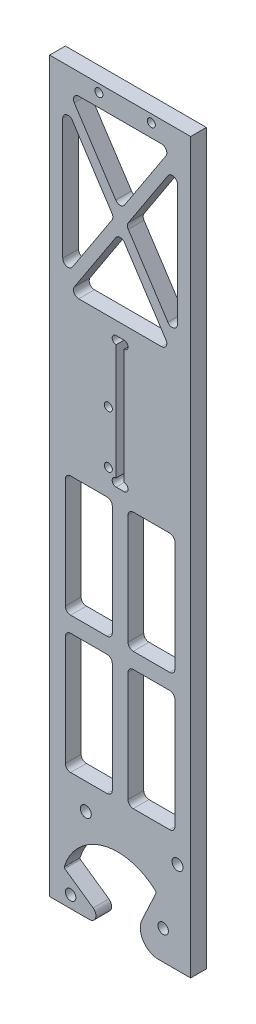
SolidWorks part; units mm, degrees
material "Thornel Mat VMA"
ref_plane "前视基准面" through (0, 0, 0) normal (0, 0, 1) x (1, 0, 0)
ref_plane "上视基准面" through (0, 0, 0) normal (0, 1, 0) x (1, 0, 0)
ref_plane "右视基准面" through (0, 0, 0) normal (1, 0, 0) x (0, 0, -1)
sketch "草图1" plane through (0, 0, 0) normal (0, 0, 1) x (1, 0, 0)
  line L1 (-33.5, 15) -> (33.5, 15)
  line L2 (-33.5, 15) -> (-33.5, -15)
  line L3 (-33.5, -15) -> (33.5, -15)
  line L4 (33.5, 15) -> (33.5, -15)
  line L5 (-33.5, 15) -> (33.5, -15) construction
  line L6 (-33.5, -15) -> (33.5, 15) construction
  point P0 (0, 0)
  dimension "D1" = 30
  dimension "D2" = 67
extrude "凸台-拉伸1" add sketch "草图1" along normal blind 6
sketch "草图3" plane through (0, 0, 6) normal (0, 0, 1) x (1, 0, 0)
  line L0 (0.156, -18.5) -> (0, 0) construction
  line L1 (33.5, -15) -> (33.5, 15) construction
  circle A0 centre (0.156, -18.5) radius 11.5
  dimension "D2" = 23
  dimension "D1" = 18.5
  dimension "D3" = 0.483
extrude "切除-拉伸1" cut sketch "草图3" against normal through all
sketch "草图4" plane through (0, 0, 6) normal (0, 0, 1) x (1, 0, 0)
  line L0 (0.156, -18.5) -> (0.156, 2.75) construction
  line L1 (14.9513, -3.2467) -> (0.156, -34.9754)
  line L2 (-20.2837, -12.6879) -> (0.156, -27)
  line L3 (0.156, -27) -> (0.156, -34.9754)
  arc A0 (14.9513, -3.2467) -> (-20.2837, -12.6879) centre (0.156, -18.5) ccw
  dimension "D1" = 42.5
  dimension "D2" = 18.5
  dimension "D3" = 27
  dimension "D4" = 34.9754
  dimension "D5" = 55
  dimension "D6" = 25
extrude "切除-拉伸2" cut sketch "草图4" against normal blind 35
sketch "草图5" plane through (0, 0, 6) normal (0, 0, 1) x (1, 0, 0)
  line L0 (-16.9818, -15) -> (-2.7003, -25)
  line L1 (-2.7003, -25) -> (-33.5, -25)
  line L2 (-33.5, -25) -> (-33.5, -15)
  line L3 (-20.2837, -12.6879) -> (-16.9818, -15) construction
  line L4 (-33.5, -15) -> (-16.9818, -15)
  line L5 (33.5, -15) -> (33.5, -25)
  line L6 (11.1104, -15) -> (33.5, -15) construction
  line L7 (33.5, -25) -> (4.8076, -25)
  line L8 (4.8076, -25) -> (10.3345, -13.1476)
  line L9 (10.3345, -13.1476) -> (14.9513, -3.2467) construction
  line L10 (33.5, -15) -> (33.5, 15) construction
  line L11 (10.3345, -13.1476) -> (33.5, -15)
  arc A0 (11.1104, -15) -> (10.3345, -13.1476) centre (0.156, -18.5) ccw construction
  dimension "D1" = 10
extrude "凸台-拉伸2" add sketch "草图5" against normal up to surface (6 mm away) up to face at (-0.3896, -5.4524, 0)
fillet "圆角1" radius 2.5 1 edges at (-2.7003, -25, 3)
fillet "圆角3" radius 0.5 2 edges at (-20.2837, -12.6879, 3) (14.9513, -3.2467, 3)
fillet "圆角4" radius 7 1 edges at (4.8076, -25, 3)
sketch "草图6" plane through (0, 0, 6) normal (0, 0, 1) x (1, 0, 0)
  line L0 (0.119, -18.5) -> (0, 0) construction
  line L1 (15.7954, -25) -> (33.5, -25) construction
  line L2 (0.119, -18.5) -> (34.657, -18.5) construction
  line L3 (17.5057, -13.8413) -> (0.119, -18.5) construction
  line L4 (-17.7824, -20.3815) -> (0.119, -18.5) construction
  circle A0 centre (0.119, -18.5) radius 18 construction
  circle A1 centre (17.5057, -13.8413) radius 2
  circle A2 centre (-17.7824, -20.3815) radius 2
  dimension "D1" = 36
  dimension "D4" = 4
  dimension "D2" = 90.369
  dimension "D3" = 18.5
  dimension "D5" = 15
  dimension "D6" = 6
extrude "切除-拉伸3" cut sketch "草图6" against normal through all
sketch "草图7" plane through (0, 0, 6) normal (0, 0, 1) x (1, 0, 0)
  line L0 (60.5, 75) -> (14.5, 75)
  line L1 (14.5, 75) -> (-16.3038, 15)
  line L4 (33.5, 15) -> (-33.5, 15) construction
  line L5 (33.5, 15) -> (60.5, 75)
  line L6 (33.5, 15) -> (-16.3038, 15)
  dimension "D1" = 49.8038
  dimension "D2" = 46
  dimension "D3" = 75
  dimension "D4" = 60.5
  dimension "D5" = 33.5
extrude "凸台-拉伸3" add sketch "草图7" against normal up to surface (6 mm away) up to face at (19.5057, -13.8413, 0)
sketch "草图8" plane through (0, 0, 6) normal (0, 0, 1) x (1, 0, 0)
  line L0 (-16.3038, 15) -> (-33.5, -18.495)
  line L1 (-33.5, 15) -> (-33.5, -25) construction
  line L2 (14.5, 75) -> (-16.3038, 15) construction
  line L3 (-33.5, 15) -> (-16.3038, 15)
  line L4 (-33.5, -18.495) -> (-33.5, 15)
extrude "切除-拉伸4" cut sketch "草图8" against normal through all
sketch "草图9" plane through (0, 0, 6) normal (0, 0, 1) x (1, 0, 0)
  line L0 (60.5, 75) -> (33.5, -25)
  line L1 (33.5, -25) -> (33.5, 15)
  line L2 (33.5, 15) -> (60.5, 75)
extrude "凸台-拉伸4" add sketch "草图9" against normal up to surface (6 mm away) up to face at (19.5057, -13.8413, 0)
sketch "草图10" plane through (0, 0, 6) normal (0, 0, 1) x (1, 0, 0)
  line L0 (-12, 10) -> (23, 10) construction
  circle A0 centre (-12, 10) radius 2.1
  circle A1 centre (23, 10) radius 2.1
  dimension "D2" = 4.2
  dimension "D1" = 10
  dimension "D3" = 12
  dimension "D4" = 35
extrude "切除-拉伸5" cut sketch "草图10" against normal through all
fillet "圆角5" radius 5 2 edges at (60.5, 75, 3) (14.5, 75, 3)
sketch "草图11" plane through (0, 0, 6) normal (0, 0, 1) x (1, 0, 0)
  line L0 (22.5, 67) -> (42.5, 67) construction
  line L1 (53.971, 75) -> (17.5535, 75) construction
  circle A0 centre (42.5, 67) radius 1.6
  circle A1 centre (22.5, 67) radius 1.6
  dimension "D3" = 3.2
  dimension "D1" = 8
  dimension "D2" = 20
  dimension "D4" = 22.5
extrude "切除-拉伸6" cut sketch "草图11" against normal through all
sketch "草图12" plane through (0, 0, 6) normal (0, 0, 1) x (1, 0, 0)
  line L16 (-8.1164, 20) -> (31.4524, 20)
  line L17 (14.4731, 64) -> (52.351, 64)
  line L18 (33.412, 64) -> (29.671, -20)
  line L19 (28.417, 64.2225) -> (24.6759, -19.7775)
  line L20 (28.417, 64.2225) -> (-8.1164, 20)
  line L21 (32.2717, 61.038) -> (-4.2616, 16.8155)
  line L24 (29.671, -20) -> (53.971, 70)
  line L25 (53.971, 70) -> (17.5535, 70)
  line L26 (17.5535, 70) -> (-18.2976, 0.1689)
  line L27 (19.3311, -5.6852) -> (13.9828, -17.1548)
  line L28 (15.7954, -20) -> (29.671, -20)
  line L29 (29.671, -20) -> (53.971, 70)
  line L30 (53.971, 70) -> (17.5535, 70)
  line L31 (17.5535, 70) -> (-18.2976, 0.1689)
  line L32 (19.3311, -5.6852) -> (13.9828, -17.1548)
  line L33 (15.7954, -20) -> (29.671, -20)
  arc A21 (18.1077, 0.652) -> (-18.2976, 0.1689) centre (0.156, -18.5) ccw
  arc A22 (19.3311, -5.6852) -> (18.1077, 0.652) centre (14.3464, -3.3608) ccw
  arc A23 (13.9828, -17.1548) -> (15.7954, -20) centre (15.7954, -18) ccw
  arc A24 (18.1077, 0.652) -> (-18.2976, 0.1689) centre (0.156, -18.5) ccw
  arc A25 (19.3311, -5.6852) -> (18.1077, 0.652) centre (14.3464, -3.3608) ccw
  arc A26 (13.9828, -17.1548) -> (15.7954, -20) centre (15.7954, -18) ccw
  dimension "D2" = 40
  dimension "D3" = 6
  dimension "D1" = 5
  dimension "D4" = 5
  dimension "D5" = 5
extrude "切除-拉伸7" cut sketch "草图12" against normal blind 10 contours L18 L29 L17 | L19 L21 L16 | L17 L31 L20
fillet "圆角6" radius 2 9 edges at (28.2332, 64, 3) (-8.1164, 20, 3) (14.4731, 64, 3) (26.4475, 20, 3) (-1.6308, 20, 3) (28.0474, 55.9246, 3) (33.412, 64, 3) (52.351, 64, 3) (29.671, -20, 3)
sketch "草图13" plane through (0, 0, 6) normal (0, 0, 1) x (1, 0, 0)
  line L0 (28, -25) -> (28, 95)
  line L1 (15.7954, -25) -> (33.5, -25) construction
  line L2 (-25.7824, -25) -> (-25.7824, 95)
  line L3 (-33.5, -25) -> (-10.6293, -25) construction
  line L4 (-25.7824, 95) -> (28, 95)
  line L5 (-25.7824, -25) -> (28, -25)
  circle A0 centre (23, 10) radius 2.1 construction
  circle A1 centre (-17.7824, -20.3815) radius 2 construction
  dimension "D1" = 5
  dimension "D2" = 8
  dimension "D3" = 120
extrude "切除-拉伸8" cut sketch "草图13" against normal blind 10 flip side to cut
sketch "草图14" plane through (0, 0, 6) normal (0, 0, 1) x (1, 0, 0)
  line L0 (-25.7824, -3.4625) -> (-25.7824, 75)
  line L1 (-25.7824, 75) -> (28, 75)
  line L2 (28, 75) -> (28, 15)
  line L3 (28, -25) -> (28, 75) construction
  line L4 (28, 15) -> (-16.3038, 15)
  line L5 (13.1054, 72.2836) -> (-25.7824, -3.4625) construction
  line L6 (-16.3038, 15) -> (-25.7824, -3.4625)
  circle A0 centre (23, 10) radius 2.1 construction
  dimension "D1" = 5
extrude "凸台-拉伸5" add sketch "草图14" against normal up to surface (6 mm away) up to face at (17.7692, 31.1403, 0)
sketch "草图15" plane through (0, 0, 6) normal (0, 0, 1) x (1, 0, 0)
  line L0 (-25.7824, 75) -> (-25.7824, 253)
  line L1 (-25.7824, 253) -> (28, 253)
  line L2 (28, 253) -> (28, 75)
  line L3 (28, 75) -> (-25.7824, 75)
  dimension "D1" = 178
extrude "凸台-拉伸6" add sketch "草图15" against normal up to surface (6 mm away) up to face at (-0.3737, -0.8234, 0)
sketch "草图16" plane through (0, 0, 6) normal (0, 0, 1) x (1, 0, 0)
  circle A0 centre (-7, 250) radius 1.5 construction
  circle A1 centre (13, 250) radius 1.5 construction
  circle A2 centre (-7, 250) radius 1.5 construction
  circle A3 centre (13, 250) radius 1.5 construction
  circle A4 centre (-7, 250) radius 1.525
  circle A5 centre (13, 250) radius 1.525
  dimension "D1" = 3.05
extrude "切除-拉伸9" cut sketch "草图16" against normal blind 10
sketch "草图17" plane through (0, 0, 6) normal (0, 0, 1) x (1, 0, 0)
  line L0 (-0.4212, 122.97) -> (2.6388, 122.97)
  line L1 (2.6388, 122.97) -> (2.6388, 173.03)
  line L2 (2.6388, 173.03) -> (-0.4212, 173.03)
  line L3 (-0.4212, 173.03) -> (-0.4212, 122.97)
  line L4 (-0.3912, 123) -> (2.6088, 123)
  line L5 (-0.3912, 173) -> (-0.3912, 123)
  line L6 (2.6088, 173) -> (-0.3912, 173)
  line L7 (2.6088, 123) -> (2.6088, 173)
  line L8 (-0.3912, 123) -> (2.6088, 123) construction
  line L9 (-0.3912, 173) -> (-0.3912, 123) construction
  line L10 (2.6088, 173) -> (-0.3912, 173) construction
  line L11 (2.6088, 123) -> (2.6088, 173) construction
  dimension "D1" = 0
  dimension "D2" = 0.03
extrude "切除-拉伸10" cut sketch "草图17" against normal up to surface (6 mm away) up to face at (-5.475, 250, 0)
sketch "草图18" plane through (0, 0, 6) normal (0, 0, 1) x (1, 0, 0)
  line L0 (2.6388, 122.97) -> (2.6388, 173.03) construction
  line L1 (-0.4212, 173.03) -> (-0.4212, 122.97) construction
  circle A0 centre (2.6388, 124.475) radius 1.505
  circle A1 centre (-0.4212, 124.475) radius 1.505
  circle A2 centre (-0.4212, 171.525) radius 1.505
  circle A3 centre (2.6388, 171.525) radius 1.505
  dimension "D1" = 3.01
extrude "切除-拉伸11" cut sketch "草图18" against normal up to surface (6 mm away) up to face at (1.1088, 148, 0)
sketch "草图19" plane through (0, 0, 6) normal (0, 0, 1) x (1, 0, 0)
  circle A0 centre (-3.3912, 128) radius 1.5 construction
  circle A1 centre (-3.3912, 148) radius 1.5 construction
  circle A2 centre (-3.3912, 128) radius 1.5 construction
  circle A3 centre (-3.3912, 148) radius 1.5 construction
  circle A4 centre (-3.3912, 148) radius 1.525
  circle A5 centre (-3.3912, 128) radius 1.525
  dimension "D1" = 3.05
extrude "切除-拉伸12" cut sketch "草图19" against normal up to surface (6 mm away) up to face at (1.1088, 148, 0)
sketch "草图20" plane through (0, 0, 6) normal (0, 0, 1) x (1, 0, 0)
  line L0 (28, -25) -> (28, 253) construction
  line L1 (-20.7824, 178.03) -> (23, 178.03)
  line L2 (-20.7824, 178.03) -> (-20.7824, 245)
  line L3 (-20.7824, 245) -> (23, 245)
  line L4 (23, 178.03) -> (23, 245)
  line L5 (-20.7824, 178.03) -> (23, 245) construction
  line L6 (-20.7824, 245) -> (23, 178.03) construction
  line L7 (-25.7824, 253) -> (-25.7824, -25) construction
  line L8 (2.6388, 173.03) -> (-0.4212, 173.03) construction
  line L9 (-19.1084, 176.9356) -> (24.674, 243.9056)
  line L10 (-22.4564, 243.9056) -> (21.326, 176.9356)
  line L11 (-22.4564, 179.1244) -> (21.326, 246.0944)
  line L12 (-19.1084, 246.0944) -> (24.674, 179.1244)
  line L13 (-0.4212, 122.97) -> (2.6388, 122.97) construction
  line L14 (-19.7824, 20) -> (22, 20)
  line L15 (-19.7824, 20) -> (-19.7824, 117.97)
  line L16 (-19.7824, 117.97) -> (22, 117.97)
  line L17 (22, 20) -> (22, 117.97)
  line L18 (-19.7824, 20) -> (22, 117.97) construction
  line L19 (-19.7824, 117.97) -> (22, 20) construction
  line L20 (-19.7824, 68.985) -> (22, 68.985) construction
  line L21 (1.1088, 117.97) -> (1.1088, 20) construction
  line L22 (-19.7824, 65.985) -> (22, 65.985)
  line L23 (-1.8912, 117.97) -> (-1.8912, 20)
  line L24 (-19.7824, 71.985) -> (22, 71.985)
  line L25 (4.1088, 117.97) -> (4.1088, 20)
  circle A0 centre (13, 250) radius 1.525 construction
  circle A1 centre (23, 10) radius 2.1 construction
  point P0 (1.1088, 211.515)
  point P21 (1.1088, 68.985)
  dimension "D1" = 5
  dimension "D2" = 5
  dimension "D3" = 5
  dimension "D4" = 5
  dimension "D7" = 6
  dimension "D8" = 6
  dimension "D9" = 5
  dimension "D10" = 10
  dimension "D5" = 2
  dimension "D6" = 2
  dimension "D11" = 3
  dimension "D12" = 3
extrude "切除-拉伸13" cut sketch "草图20" against normal blind 10 contours L16 L25 L24 L17 | L22 L25 L14 L17 | L23 L22 L15 L14 | L15 L24 L23 L16 | L10 L9 L1 | L9 L12 L4 | L2 L11 L10 | L3 L12 L11
fillet "圆角7" radius 2 28 edges at (22, 65.985, 3) (22, 20, 3) (4.1088, 20, 3) (4.1088, 65.985, 3) (-19.7824, 117.97, 3) (-1.8912, 117.97, 3) (20.6105, 245, 3) (1.1088, 215.17, 3) (-18.3929, 245, 3) (23, 241.345, 3) (23, 181.685, 3) (3.4983, 211.515, 3) (22, 117.97, 3) (22, 71.985, 3) (4.1088, 71.985, 3) (4.1088, 117.97, 3) (-20.7824, 241.345, 3) (-1.2807, 211.515, 3) (-20.7824, 181.685, 3) (20.6105, 178.03, 3) (-18.3929, 178.03, 3) (1.1088, 207.86, 3) (-1.8912, 20, 3) (-19.7824, 20, 3) (-19.7824, 65.985, 3) (-1.8912, 65.985, 3) (-1.8912, 71.985, 3) (-19.7824, 71.985, 3)
